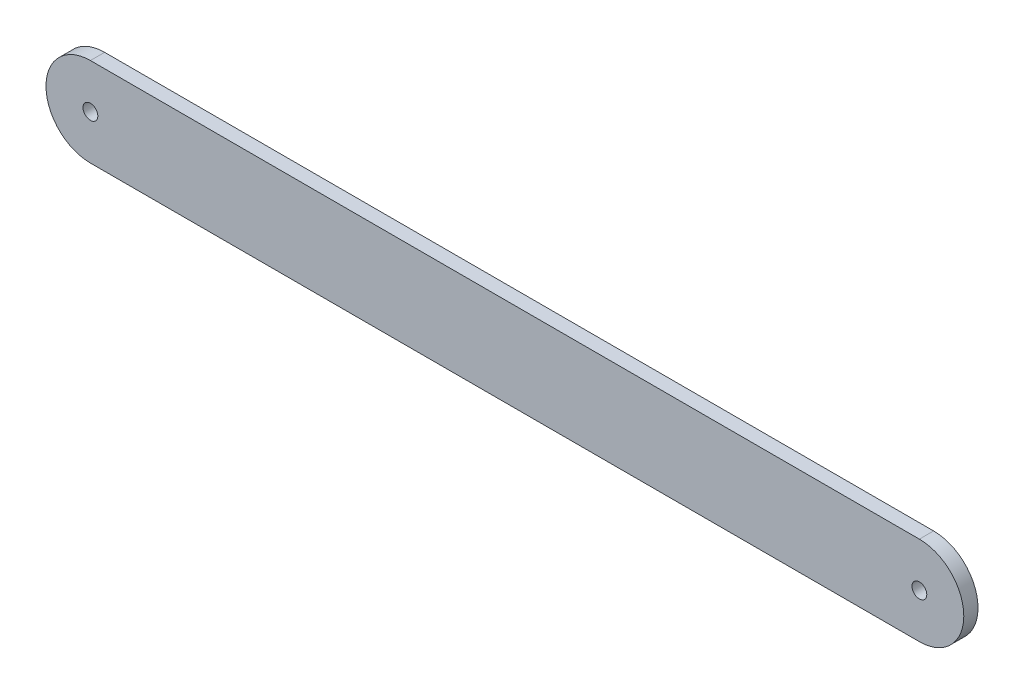
SolidWorks part; units mm, degrees
ref_plane "Front Plane" through (0, 0, 0) normal (0, 0, 1) x (1, 0, 0)
ref_plane "Top Plane" through (0, 0, 0) normal (0, 1, 0) x (1, 0, 0)
ref_plane "Right Plane" through (0, 0, 0) normal (1, 0, 0) x (0, 0, -1)
sketch "Sketch1" plane through (0, 0, 0) normal (0, 0, 1) x (1, 0, 0)
  line L0 (0, 0) -> (177.8, 0) construction
  line L1 (0, 0) -> (177.8, 0) construction
  line L2 (0, 9.525) -> (177.8, 9.525)
  line L3 (0, -9.525) -> (177.8, -9.525)
  circle A0 centre (0, 0) radius 1.5875
  circle A1 centre (177.8, 0) radius 1.5875
  arc A2 (0, 9.525) -> (0, -9.525) centre (0, 0) ccw
  arc A3 (177.8, -9.525) -> (177.8, 9.525) centre (177.8, 0) ccw
  point P5 (88.9, 0)
  dimension "D1" = 3.175
  dimension "D3" = 3.175
  dimension "D2" = 177.8
  dimension "D4" = 19.05
extrude "Boss-Extrude1" add sketch "Sketch1" along normal blind 3.048
sketch "Sketch2" [suppressed] plane through (0, 0, 0) normal (0, 0, 1) x (1, 0, 0)
  line L0 (0, 0) -> (101.6, 0) construction
  line L1 (0, 0) -> (101.6, 0) construction
  line L2 (0, 9.525) -> (101.6, 9.525)
  line L3 (0, -9.525) -> (101.6, -9.525)
  circle A0 centre (0, 0) radius 1.5875
  circle A1 centre (101.6, 0) radius 1.5875
  arc A2 (0, 9.525) -> (0, -9.525) centre (0, 0) ccw
  arc A3 (101.6, -9.525) -> (101.6, 9.525) centre (101.6, 0) ccw
  point P5 (50.8, 0)
  dimension "D1" = 3.175
  dimension "D3" = 3.175
  dimension "D2" = 101.6
  dimension "D4" = 19.05
extrude "Boss-Extrude2" [suppressed] add sketch "Sketch2" along normal blind 3.048
sketch "Sketch3" [suppressed] plane through (0, 0, 0) normal (0, 0, 1) x (1, 0, 0)
  line L0 (0, 0) -> (177.8, 0) construction
  line L1 (0, 0) -> (177.8, 0) construction
  line L2 (0, 9.525) -> (177.8, 9.525)
  line L3 (0, -9.525) -> (177.8, -9.525)
  circle A0 centre (0, 0) radius 1.5875
  circle A1 centre (177.8, 0) radius 1.5875
  arc A2 (0, 9.525) -> (0, -9.525) centre (0, 0) ccw
  arc A3 (177.8, -9.525) -> (177.8, 9.525) centre (177.8, 0) ccw
  point P5 (88.9, 0)
  dimension "D1" = 3.175
  dimension "D3" = 3.175
  dimension "D2" = 177.8
  dimension "D4" = 19.05
extrude "Boss-Extrude3" [suppressed] add sketch "Sketch3" along normal blind 3.048
sketch "Sketch4" [suppressed] plane through (0, 0, 0) normal (0, 0, 1) x (1, 0, 0)
  line L0 (0, 0) -> (157.988, 0) construction
  line L1 (0, 0) -> (157.988, 0) construction
  line L2 (0, 9.525) -> (157.988, 9.525)
  line L3 (0, -9.525) -> (157.988, -9.525)
  circle A0 centre (0, 0) radius 1.5875
  circle A1 centre (157.988, 0) radius 1.5875
  arc A2 (0, 9.525) -> (0, -9.525) centre (0, 0) ccw
  arc A3 (157.988, -9.525) -> (157.988, 9.525) centre (157.988, 0) ccw
  point P5 (78.994, 0)
  dimension "D1" = 3.175
  dimension "D3" = 3.175
  dimension "D2" = 157.988
  dimension "D4" = 19.05
extrude "Boss-Extrude4" [suppressed] add sketch "Sketch4" along normal blind 3.048
sketch "Sketch6" [suppressed] plane through (0, 0, 3.048) normal (0, 0, 1) x (1, 0, 0)
  line L0 (0, -9.525) -> (177.8, -9.525) construction
  line L1 (177.8, 9.525) -> (0, 9.525) construction
  line L2 (161.925, -9.525) -> (177.8, -9.525)
  line L3 (177.8, 9.525) -> (161.925, 9.525)
  line L4 (161.925, 9.525) -> (161.925, -9.525)
  arc A0 (177.8, -9.525) -> (177.8, 9.525) centre (177.8, 0) ccw construction
  arc A1 (177.8, -9.525) -> (177.8, 9.525) centre (177.8, 0) ccw
  circle A2 centre (177.8, 0) radius 1.5875 construction
  circle A3 centre (177.8, 0) radius 1.5875
  point P7 (187.325, 0)
  dimension "D1" = 25.4
extrude "Boss-Extrude5" [suppressed] add sketch "Sketch6" along normal blind 2.54
fillet "Fillet1" [suppressed] radius 2.54
fillet "Fillet2" [suppressed] radius 2.54
sketch "Sketch5" [suppressed] plane through (0, 0, 3.048) normal (0, 0, 1) x (1, 0, 0)
  line L0 (177.8, 2.667) -> (177.8, 12.7) construction
  line L1 (177.8, -2.667) -> (177.8, -11.2306) construction
  line L2 (177.8, 12.7) -> (177.8, 2.667) construction
  line L3 (180.467, 12.7) -> (180.467, 2.667)
  line L4 (175.133, 12.7) -> (175.133, 2.667)
  line L5 (190.5, 2.667) -> (180.467, 2.667)
  line L6 (190.5, -2.667) -> (180.467, -2.667)
  line L7 (190.5, 0) -> (177.8, 0) construction
  line L8 (180.467, -12.7) -> (180.467, -2.667)
  line L9 (175.133, -12.7) -> (175.133, -2.667)
  line L10 (177.8, -12.7) -> (177.8, -2.667) construction
  line L11 (165.1, -2.667) -> (175.133, -2.667)
  line L12 (165.1, 2.667) -> (175.133, 2.667)
  line L13 (165.1, 0) -> (177.8, 0) construction
  arc A0 (180.467, 12.7) -> (175.133, 12.7) centre (177.8, 12.7) ccw
  arc A2 (190.5, -2.667) -> (190.5, 2.667) centre (190.5, 0) ccw
  arc A4 (175.133, -12.7) -> (180.467, -12.7) centre (177.8, -12.7) ccw
  arc A6 (165.1, 2.667) -> (165.1, -2.667) centre (165.1, 0) ccw
  point P4 (177.8, 6.35)
  point P13 (184.15, 0)
  point P19 (177.8, -6.35)
  point P25 (171.45, 0)
  point P30 (177.8, 0)
  dimension "D1" = 5.334
  dimension "D2" = 12.7
  dimension "D3" = 4
extrude "Cut-Extrude2" [suppressed] cut sketch "Sketch5" along normal blind 2.54 contours L5 L3 A0 L4 L12 A6 L11 L9 A4 L8 L6 A2
fillet "Fillet3" [suppressed] radius 0.508
sketch "Sketch7" [suppressed] plane through (0, 0, 3.048) normal (0, 0, 1) x (1, 0, 0)
  line L0 (133.985, 9.525) -> (133.985, -9.525)
  line L3 (0, -9.525) -> (159.385, -9.525)
  line L4 (159.385, -9.525) -> (159.385, 9.525)
  line L5 (159.385, 9.525) -> (0, 9.525)
  line L6 (0, -9.525) -> (133.985, -9.525)
  line L8 (133.985, 9.525) -> (0, 9.525)
  arc A1 (0, 9.525) -> (0, -9.525) centre (0, 0) ccw
  arc A2 (0, 9.525) -> (0, -9.525) centre (0, 0) ccw
  dimension "D2" = 25.4
  dimension "D1" = 0
extrude "Cut-Extrude3" [suppressed] cut sketch "Sketch7" against normal through all
sketch "Sketch11" [suppressed] plane through (0, 0, 3.048) normal (0, 0, 1) x (1, 0, 0)
  line L0 (52.7467, 0) -> (0, 0) construction
  line L1 (65.6499, 5.8166) -> (52.7467, 5.8166)
  line L2 (65.6499, 5.8166) -> (65.6499, -5.8166)
  line L3 (65.6499, -5.8166) -> (52.7467, -5.8166)
  line L4 (52.7467, 5.8166) -> (52.7467, -5.8166)
  dimension "D1" = 52.7467
  dimension "D2" = 11.6332
  dimension "D3" = 12.9032
extrude "Cut-Extrude4" [suppressed] cut sketch "Sketch11" against normal through all contours L2 L3 L4 L1
